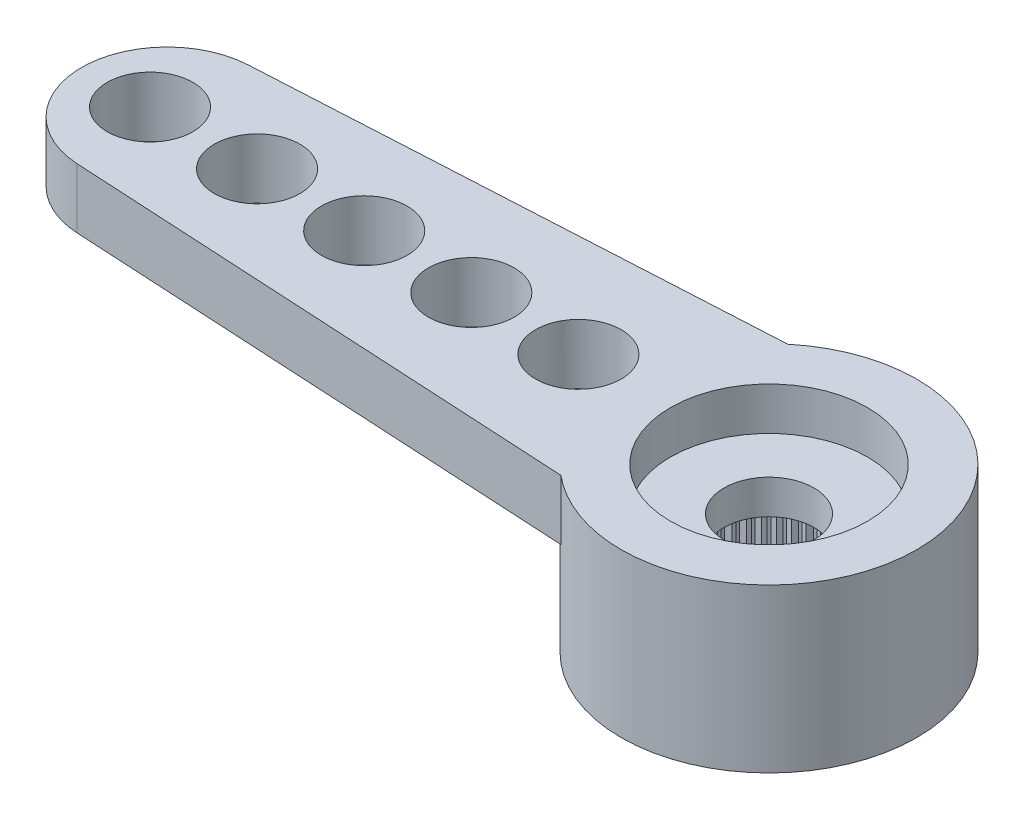
SolidWorks part; units mm, degrees
material "PVC Rígido"
ref_plane "Plano frontal" through (0, 0, 0) normal (0, 0, 1) x (1, 0, 0)
ref_plane "Plano superior" through (0, 0, 0) normal (0, 1, 0) x (1, 0, 0)
ref_plane "Plano direito" through (0, 0, 0) normal (1, 0, 0) x (0, 0, -1)
sketch "Esboço1" plane through (0, 0, 0) normal (0, 1, 0) x (1, 0, 0)
  line L0 (0, 0) -> (-14.05, 0) construction
  line L1 (-14.1591, 1.997) -> (-2.2091, 2.65)
  line L2 (-2.2091, -2.65) -> (-14.1591, -1.997)
  arc A0 (-2.2091, -2.65) -> (-2.2091, 2.65) centre (0, 0) ccw
  arc A1 (-14.1591, 1.997) -> (-14.1591, -1.997) centre (-14.05, 0) ccw
  dimension "D1" = 6.9
  dimension "D2" = 4
  dimension "D3" = 19.5
  dimension "D4" = 5.3
extrude "Ressalto-extrusão1" add sketch "Esboço1" against normal blind 1.4
sketch "Esboço2" plane through (0, -1.4, 0) normal (0, -1, 0) x (1, 0, 0)
  arc A0 (-2.2091, -2.65) -> (-2.2091, 2.65) centre (0, 0) ccw construction
  circle A1 centre (0, 0) radius 3.45
extrude "Ressalto-extrusão2" add sketch "Esboço2" along normal offset from surface (2.4 mm away) 3.8 up to face at (-7.242, 0, 0)
hole_wizard "Furo4" positions "Esboço9" profile "Esboço10" legacy end condition through all
sketch "Esboço9" plane through (0, 0, 0) normal (0, 1, 0) x (1, 0, 0)
  line L1 (-14.45, 0) -> (0, 0) construction
  arc A2 (-14.1591, 1.997) -> (-14.1591, -1.997) centre (-14.05, 0) ccw construction
  point P0 (-14.45, 0)
  point P19 (-16.05, 0)
  dimension "D1" = 1.6
sketch "Esboço10" plane through (-14.45, 0, 0) normal (1, 0, 0) x (0, 0, 1)
  line L0 (0, 0) -> (0, 3.8)
  line L1 (0, 3.8) -> (1, 3.8)
  line L2 (1, 3.8) -> (1, 0)
  line L3 (1, 0) -> (0, 0)
  line L4 (0, 110) -> (0, -10) construction
  dimension "Diameter" = 2
  dimension "Depth" = 3.8
pattern_linear "Padrão linear1" count 5 spacing 2.5 along (1, 0, 0) of "Furo4"
hole_wizard "Furo1" positions "Esboço3" profile "Esboço4" legacy
sketch "Esboço3" plane through (0, -3.8, 0) normal (0, -1, 0) x (-1, 0, 0)
  point P0 (0, 0)
sketch "Esboço4" plane through (0, -3.8, 0) normal (1, 0, 0) x (0, 0, -1)
  line L0 (0, 0) -> (0, 2)
  line L1 (0, 2) -> (2.475, 2)
  line L2 (2.475, 2) -> (2.475, 0)
  line L3 (2.475, 0) -> (0, 0)
  line L4 (0, 110) -> (0, -10) construction
  dimension "Diameter" = 4.95
  dimension "Depth" = 2
hole_wizard "Furo2" positions "Esboço5" profile "Esboço6" legacy
sketch "Esboço5" plane through (0, 0, 0) normal (0, 1, 0) x (1, 0, 0)
  point P0 (0, 0)
sketch "Esboço6" plane through (0, 0, 0) normal (1, 0, 0) x (0, 0, 1)
  line L0 (0, 0) -> (0, 1)
  line L1 (0, 1) -> (2.3, 1)
  line L2 (2.3, 1) -> (2.3, 0)
  line L3 (2.3, 0) -> (0, 0)
  line L4 (0, 110) -> (0, -10) construction
  dimension "Diameter" = 4.6
  dimension "Depth" = 1
hole_wizard "Furo3" positions "Esboço7" profile "Esboço8" legacy end condition through all
sketch "Esboço7" plane through (0, 0, 0) normal (0, 1, 0) x (1, 0, 0)
  point P0 (0, 0)
sketch "Esboço8" plane through (0, 0, 0) normal (1, 0, 0) x (0, 0, 1)
  line L0 (0, 0) -> (0, 3.8)
  line L1 (0, 3.8) -> (1.05, 3.8)
  line L2 (1.05, 3.8) -> (1.05, 0)
  line L3 (1.05, 0) -> (0, 0)
  line L4 (0, 110) -> (0, -10) construction
  dimension "Diameter" = 2.1
  dimension "Depth" = 3.8
sketch "Esboço11" plane through (0, -3.8, 0) normal (0, -1, 0) x (1, 0, 0)
  line L0 (-0.0981, 2.4731) -> (0, 2.375)
  line L1 (0, 2.375) -> (0.0981, 2.4731)
  line L2 (0, 0) -> (0, 2.475) construction
  circle A0 centre (0, 0) radius 2.375 construction
  circle A1 centre (0, 0) radius 2.475
  arc A2 (0.0981, 2.4731) -> (-0.0981, 2.4731) centre (0, 0) ccw
  dimension "D3" = 4.75
  dimension "D2" = 0.1
  dimension "D1" = 0
extrude "Ressalto-extrusão3" add sketch "Esboço11" against normal up to surface (2 mm away) up to face at (0, -1.8, 1.05)
pattern_circular "PadrãoCircular1" count 60 over 360 about axis through (0, 0, 0) along (0, 1, 0) of "Ressalto-extrusão3"
